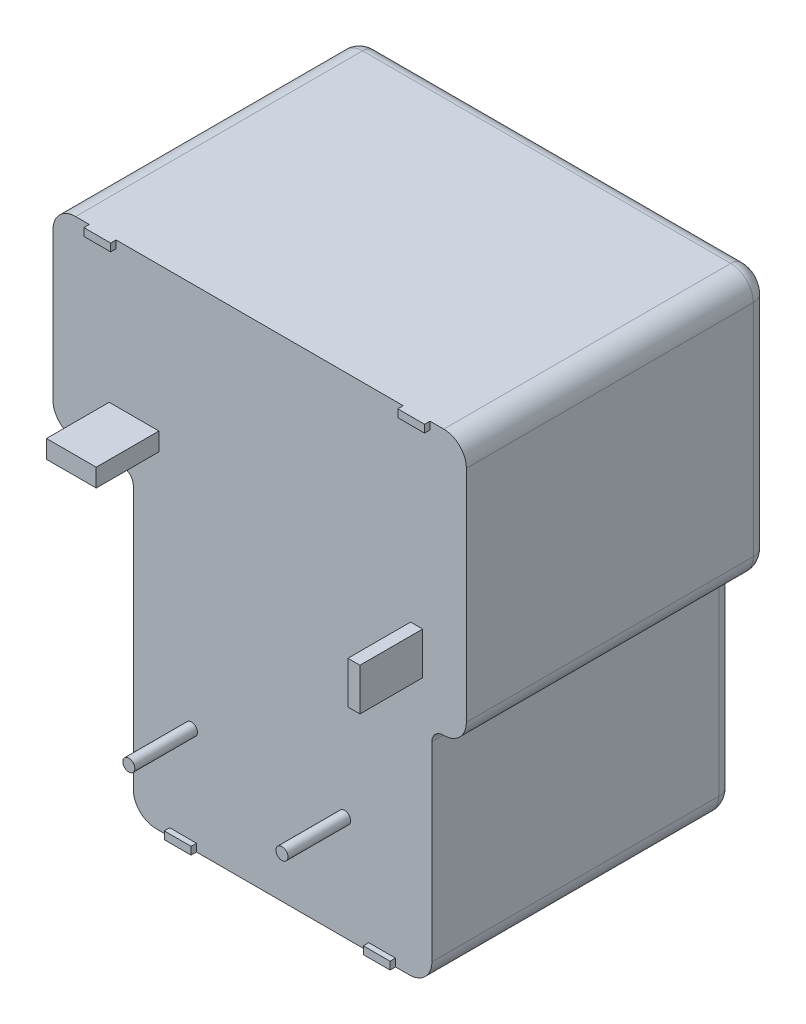
SolidWorks part; units mm, degrees
ref_plane "Front Plane" through (0, 0, 0) normal (0, 0, 1) x (1, 0, 0)
ref_plane "Top Plane" through (0, 0, 0) normal (0, 1, 0) x (1, 0, 0)
ref_plane "Right Plane" through (0, 0, 0) normal (1, 0, 0) x (0, 0, -1)
ref_plane "Plane1" through (0, 0, -20.0406) normal (0, 0, -1) x (-1, 0, 0)
sketch "Sketch1" plane through (0, 0, -20.0406) normal (0, 0, -1) x (-1, 0, 0)
  line L0 (-13.2568, 16.255) -> (-13.2568, -16.255)
  line L1 (-13.2568, -16.255) -> (14.1732, -16.255)
  line L2 (14.1732, -16.255) -> (14.1732, 16.255)
  line L3 (14.1732, 16.255) -> (-13.2568, 16.255)
extrude "Boss-Extrude1" add sketch "Sketch1" against normal blind 20.0406
sketch "Sketch2" plane through (0, 0, 0) normal (0, 0, 1) x (1, 0, 0)
  line L0 (-8.8412, 3.455) -> (-14.1732, 3.455)
  line L1 (-14.1732, 3.455) -> (-14.1732, -16.255)
  line L2 (-14.1732, -16.255) -> (-8.8412, -16.255)
  line L3 (-8.8412, -16.255) -> (-8.8412, 3.455)
extrude "Cut-Extrude1" cut sketch "Sketch2" against normal through all
sketch "Sketch3" plane through (0, 0, 0) normal (0, 0, 1) x (1, 0, 0)
  line L0 (13.2568, -1.345) -> (10.9708, -1.345)
  line L1 (10.9708, -1.345) -> (10.9708, -16.255)
  line L2 (10.9708, -16.255) -> (13.2568, -16.255)
  line L3 (13.2568, -16.255) -> (13.2568, -1.345)
extrude "Cut-Extrude2" cut sketch "Sketch3" against normal through all
sketch "Sketch4" plane through (0, 0, 0) normal (0, 0, 1) x (1, 0, 0)
  line L0 (-7.1432, 6.695) -> (-7.1432, 5.495)
  line L1 (-7.1432, 5.495) -> (-10.4432, 5.495)
  line L2 (-10.4432, 5.495) -> (-10.4432, 6.695)
  line L3 (-10.4432, 6.695) -> (-7.1432, 6.695)
extrude "Boss-Extrude2" add sketch "Sketch4" along normal blind 4.1594 separate body
sketch "Sketch5" plane through (0, 0, 0) normal (0, 0, 1) x (1, 0, 0)
  line L0 (10.3568, 4.065) -> (10.3568, 1.265)
  line L1 (10.3568, 1.265) -> (9.5568, 1.265)
  line L2 (9.5568, 1.265) -> (9.5568, 4.065)
  line L3 (9.5568, 4.065) -> (10.3568, 4.065)
extrude "Boss-Extrude3" add sketch "Sketch5" along normal blind 4.1594 separate body
sketch "Sketch6" plane through (0, 0, 0) normal (0, 0, 1) x (1, 0, 0)
  circle A0 centre (-4.9832, -9.345) radius 0.4
extrude "Boss-Extrude4" add sketch "Sketch6" along normal blind 4.1594 separate body
sketch "Sketch7" plane through (0, 0, 0) normal (0, 0, 1) x (1, 0, 0)
  line L0 (10.8438, 16.255) -> (10.8438, 15.747)
  line L1 (10.8438, 15.747) -> (9.0658, 15.747)
  line L2 (9.0658, 15.747) -> (9.0658, 16.255)
  line L3 (9.0658, 16.255) -> (10.8438, 16.255)
extrude "Boss-Extrude5" add sketch "Sketch7" along normal blind 0.3594
sketch "Sketch8" plane through (0, 0, 0) normal (0, 0, 1) x (1, 0, 0)
  line L0 (-11.7602, 16.255) -> (-9.9822, 16.255)
  line L1 (-9.9822, 16.255) -> (-9.9822, 15.747)
  line L2 (-9.9822, 15.747) -> (-11.7602, 15.747)
  line L3 (-11.7602, 15.747) -> (-11.7602, 16.255)
extrude "Boss-Extrude6" add sketch "Sketch8" along normal blind 0.3594
sketch "Sketch9" plane through (0, 0, 0) normal (0, 0, 1) x (1, 0, 0)
  line L0 (-6.4282, -16.255) -> (-6.4282, -15.747)
  line L1 (-6.4282, -15.747) -> (-4.6502, -15.747)
  line L2 (-4.6502, -15.747) -> (-4.6502, -16.255)
  line L3 (-4.6502, -16.255) -> (-6.4282, -16.255)
extrude "Boss-Extrude7" add sketch "Sketch9" along normal blind 0.3594
sketch "Sketch10" plane through (0, 0, 0) normal (0, 0, 1) x (1, 0, 0)
  line L0 (8.5578, -16.255) -> (6.7798, -16.255)
  line L1 (6.7798, -16.255) -> (6.7798, -15.747)
  line L2 (6.7798, -15.747) -> (8.5578, -15.747)
  line L3 (8.5578, -15.747) -> (8.5578, -16.255)
extrude "Boss-Extrude8" add sketch "Sketch10" along normal blind 0.3594
sketch "Sketch11" plane through (0, 0, 0) normal (0, 0, 1) x (1, 0, 0)
  circle A0 centre (5.1768, -9.345) radius 0.4
extrude "Boss-Extrude9" add sketch "Sketch11" along normal blind 4.1594 separate body
fillet "Fillet1" radius 1.5001 6 edges at (10.9708, -16.255, -10.0203) (13.2568, 16.255, -10.0203) (13.2568, -1.345, -10.0203) (-14.1732, 16.255, -10.0203) (-8.8412, -16.255, -10.0203) (-14.1732, 3.455, -10.0203)
fillet "Fillet2" radius 0.762 2 edges at (10.9708, -1.345, -10.0203) (-8.8412, 3.455, -10.0203)
fillet "Fillet3" radius 1 16 edges at (13.2568, 7.455, -20.0406) (12.8174, -0.9056, -20.0406) (12.8174, 15.8156, -20.0406) (11.7447, -1.345, -20.0406) (-0.4582, 16.255, -20.0406) (11.194, -1.5682, -20.0406) (-13.7338, 15.8156, -20.0406) (10.9708, -8.4309, -20.0406) (-14.1732, 9.855, -20.0406) (10.5314, -15.8156, -20.0406) (-13.7338, 3.8944, -20.0406) (1.0648, -16.255, -20.0406) (-11.1381, 3.455, -20.0406) (-8.4018, -15.8156, -20.0406) (-9.0644, 3.2318, -20.0406) (-8.8412, -6.0309, -20.0406)
